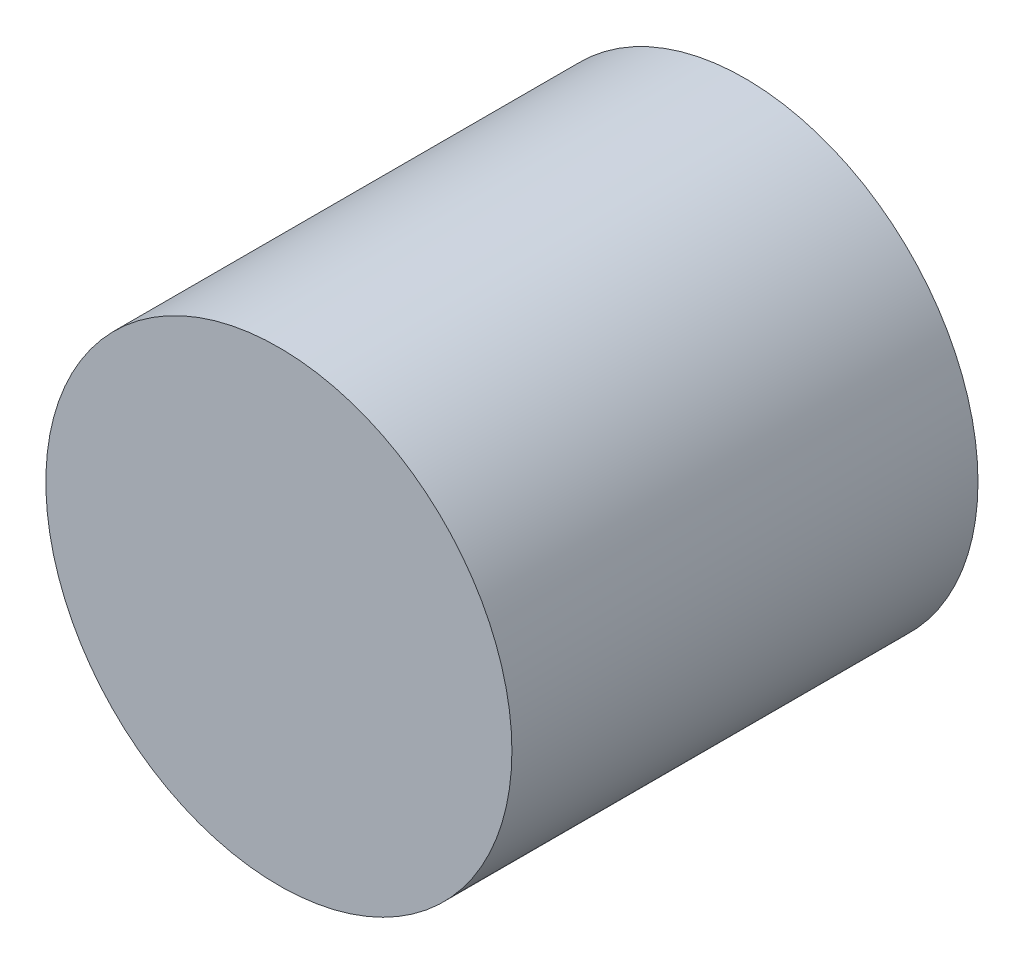
SolidWorks part; units mm, degrees
ref_plane "Front Plane" through (0, 0, 0) normal (0, 0, 1) x (1, 0, 0)
ref_plane "Top Plane" through (0, 0, 0) normal (0, 1, 0) x (1, 0, 0)
ref_plane "Right Plane" through (0, 0, 0) normal (1, 0, 0) x (0, 0, -1)
sketch "Sketch3" plane through (0, 0, 0) normal (0, 0, 1) x (1, 0, 0)
  line L0 (0, 0) -> (-5.4505, 0) construction
  line L1 (-5.4505, 0) -> (5.3154, 0) construction
  line L2 (5.3154, 0) -> (0, 0) construction
  line L3 (0, 0) -> (0, 4.5158) construction
  line L4 (0, 4.5158) -> (0, -2.2185) construction
  line L5 (0, -2.2185) -> (0, -4.4257) construction
  circle A0 centre (0, 0) radius 2
  dimension "D1" = 4
extrude "Boss-Extrude1" add sketch "Sketch3" along normal blind 4
